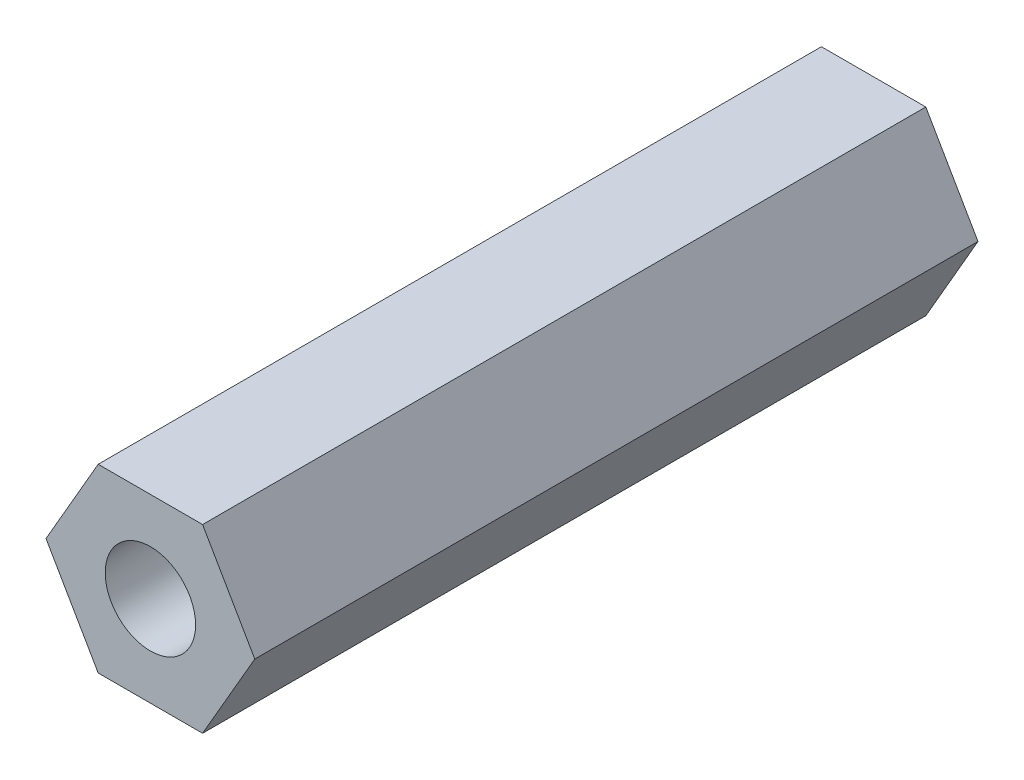
SolidWorks part; units mm, degrees
material "6061 合金"
ref_plane "前视基准面" through (0, 0, 0) normal (0, 0, 1) x (1, 0, 0)
ref_plane "上视基准面" through (0, 0, 0) normal (0, 1, 0) x (1, 0, 0)
ref_plane "右视基准面" through (0, 0, 0) normal (1, 0, 0) x (0, 0, -1)
sketch "草图1" plane through (0, 0, 0) normal (0, 0, 1) x (1, 0, 0)
  line L1 (1.4434, 2.5) -> (-1.4434, 2.5)
  line L2 (-1.4434, 2.5) -> (-2.8868, 0)
  line L3 (-2.8868, 0) -> (-1.4434, -2.5)
  line L4 (-1.4434, -2.5) -> (1.4434, -2.5)
  line L5 (1.4434, -2.5) -> (2.8868, 0)
  line L6 (2.8868, 0) -> (1.4434, 2.5)
  circle A0 centre (0, 0) radius 2.5 construction
  dimension "D1" = 5
extrude "凸台-拉伸1" add sketch "草图1" along normal blind 20
hole_wizard "M3 螺纹孔1" positions "草图2" profile "草图3" tap size "M3" standard "GB" end condition through all
sketch "草图2" plane through (0, 0, 20) normal (0, 0, 1) x (1, 0, 0)
  point P0 (0, 0)
sketch "草图3" plane through (0, 0, 20) normal (1, 0, 0) x (0, -1, 0)
  line L0 (0, 0) -> (0, 20)
  line L1 (0, 20) -> (1.25, 20)
  line L2 (1.25, 20) -> (1.25, 0)
  line L5 (1.25, 0) -> (0, 0)
  line L11 (0, -6.35) -> (0, 107.95) construction
  dimension "通孔螺纹孔钻头直径" = 2.5
  dimension "通孔螺纹孔钻头深度" = 20
cosmetic thread "孔螺蚊线1" parameters "D2"=3
